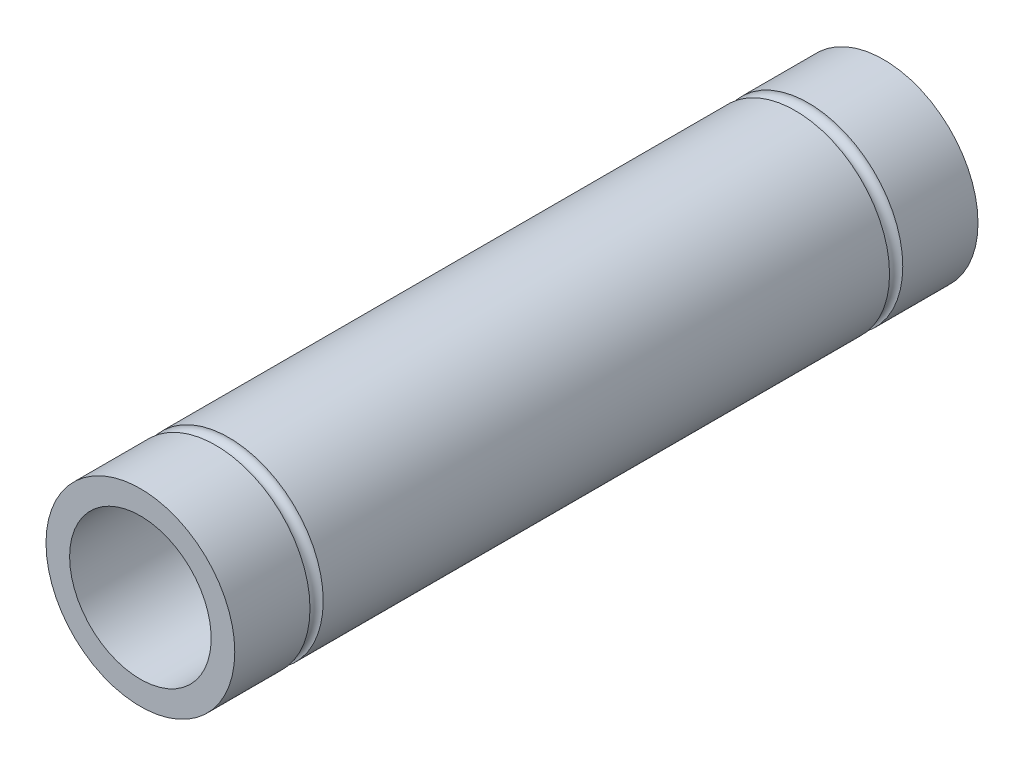
SolidWorks part; units mm, degrees
material "6061-T6 (SS)"
ref_plane "Front Plane" through (0, 0, 0) normal (0, 0, 1) x (1, 0, 0)
ref_plane "Top Plane" through (0, 0, 0) normal (0, 1, 0) x (1, 0, 0)
ref_plane "Right Plane" through (0, 0, 0) normal (1, 0, 0) x (0, 0, -1)
sketch "Sketch1" plane through (0, 0, 0) normal (0, 0, 1) x (1, 0, 0)
  line L0 (6.1484, 1.5875) -> (3.8624, 1.5875)
  line L1 (3.8624, 1.5875) -> (3.8624, -1.5875)
  line L2 (3.8624, -1.5875) -> (6.1484, -1.5875)
  arc A1 (6.1484, 1.5875) -> (6.1484, -1.5875) centre (0, 0) ccw
  arc A2 (6.1484, 1.5875) -> (6.1484, -1.5875) centre (0, 0) cw
  dimension "D1" = 6.35
  dimension "D2" = 3.175
  dimension "D3" = 2.286
extrude "Boss-Extrude1" add sketch "Sketch1" along normal blind 50 contours L0 A1 L2 L1 | A2 L0 L1 L2
hole_wizard "3/8 (0.3750) Dowel Hole1" positions "Sketch2" profile "Sketch3" hole size "3/8" standard "ANSI Inch" end condition through all
sketch "Sketch2" plane through (0, 0, 0) normal (0, 0, 1) x (1, 0, 0)
  point P0 (0, 0)
sketch "Sketch3" plane through (0, 0, 0) normal (1, 0, 0) x (0, 1, 0)
  line L0 (0, 0) -> (0, 50)
  line L1 (0, 50) -> (4.7625, 50)
  line L2 (4.7625, 50) -> (4.7625, 0)
  line L5 (4.7625, 0) -> (0, 0)
  line L11 (0, -6.35) -> (0, 107.95) construction
  dimension "Thru Hole Dia." = 9.525
  dimension "Thru Hole Depth" = 50
sketch "Sketch5" plane through (0, 0, 0) normal (0, 1, 0) x (1, 0, 0)
  line L0 (0, -50) -> (0, 0) construction
  line L1 (-6.35, -50) -> (6.35, -50) construction
  line L2 (-6.35, -25) -> (6.35, -25) construction
  line L3 (-6.35, 0) -> (-6.35, -50) construction
  line L4 (6.35, -50) -> (6.35, 0) construction
  line L5 (-6.35, -5.95) -> (-6.35, -5.061)
  line L6 (6.35, -5.95) -> (6.35, -5.061)
  line L7 (-6.35, -44.05) -> (-6.35, -44.939)
  arc A0 (-6.35, -5.95) -> (-6.35, -5.061) centre (-6.35, -5.5055) ccw
  arc A1 (6.35, -5.95) -> (6.35, -5.061) centre (6.35, -5.5055) cw
  arc A2 (-6.35, -44.05) -> (-6.35, -44.939) centre (-6.35, -44.4945) cw
  point P11 (-6.35, -5.95)
  point P12 (-6.35, -44.05)
  point P16 (-5.9055, -5.5055)
  point P20 (5.9055, -5.5055)
  dimension "D2" = 0.889
  dimension "D1" = 38.1
revolve "Cut-Revolve1" cut sketch "Sketch5" angle 360 about L0
